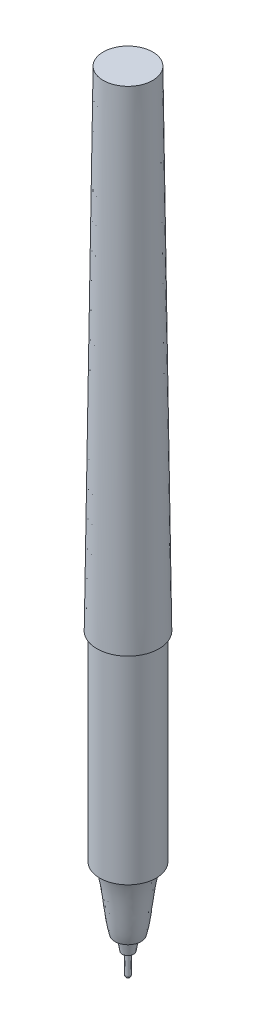
SolidWorks part; units mm, degrees
ref_plane "Front Plane" through (0, 0, 0) normal (0, 0, 1) x (1, 0, 0)
ref_plane "Top Plane" through (0, 0, 0) normal (0, 1, 0) x (1, 0, 0)
ref_plane "Right Plane" through (0, 0, 0) normal (1, 0, 0) x (0, 0, -1)
sketch "Sketch1" plane through (0, 0, 0) normal (0, 1, 0) x (1, 0, 0)
  circle A0 centre (0, 0) radius 4.9911
  dimension "D1" = 9.9822
sketch3d "3DSketch1" plane through (0, 0, 0) normal (0, 0, 1) x (1, 0, 0)
  dimension "D1" = 78.74
sketch "Sketch8" plane through (0, 0, 0) normal (1, 0, 0) x (0, 0, -1)
  line L0 (0, -1000) -> (0, 49000) construction
sketch "Sketch9" plane through (0, 78.74, 0) normal (0, 1, 0) x (-1, 0, 0)
  circle A0 centre (0, 0) radius 3.9782
  dimension "D1" = 7.9565
loft "Loft2" add profiles "Sketch1", "Sketch9"
sketch "Sketch11" plane through (0, 0, 0) normal (0, -1, 0) x (1, 0, 0)
  circle A0 centre (0, 0) radius 4.5466
  dimension "D1" = 9.0932
extrude "Boss-Extrude6" add sketch "Sketch11" along normal blind 32.1945
sketch "Sketch12" plane through (0, 0, 0) normal (0, 0, 1) x (1, 0, 0)
  line L0 (0, -201000) -> (0, 249000) construction
  line L1 (0, -32.1945) -> (3.8608, -32.1945)
  line L2 (-4.5466, -32.1945) -> (4.5466, -32.1945) construction
  line L3 (0, -42.2783) -> (2.1019, -42.2783)
  line L4 (0, -32.1945) -> (0, -42.2783)
  spline S0 degree 3 poles (3.8608, -32.1945) (2.8705, -34.9719) (2.8125, -39.8412) (2.1018, -42.2783) knots 0 0 0 0 1 1 1 1
  dimension "D3" = 10.0838
  dimension "D1" = 3.8608
  dimension "D2" = 2.1019
revolve "Revolve1" add sketch "Sketch12" angle 360 about L0
sketch "Sketch13" plane through (0, 0, 0) normal (0, 0, 1) x (1, 0, 0)
  line L0 (0, -42.2783) -> (1.3144, -42.2783)
  line L1 (-2.1018, -42.2783) -> (2.1018, -42.2783) construction
  line L2 (1.3144, -42.2783) -> (0.9207, -44.6278)
  line L3 (0.9207, -44.6278) -> (0, -44.6278)
  line L4 (0, -201000) -> (0, 249000) construction
  line L5 (0, -42.2783) -> (0, -44.6278)
  dimension "D1" = 1.3144
  dimension "D2" = 0.9207
  dimension "D3" = 2.3495
revolve "Revolve2" add sketch "Sketch13" angle 360 about L0
sketch "Sketch14" plane through (0, 0, 0) normal (0, 0, 1) x (1, 0, 0)
  line L0 (0, -44.6278) -> (0.4001, -44.6278)
  line L1 (0, -201000) -> (0, 249000) construction
  line L2 (0.4001, -44.6278) -> (0.4001, -47.9044)
  line L3 (-0.9207, -44.6278) -> (0.9207, -44.6278) construction
  line L4 (0, -44.6278) -> (0, -48.3108)
  arc A0 (0.4001, -47.9044) -> (0, -48.3108) centre (-0.0063, -47.9044) cw
  dimension "D2" = 0.4064
  dimension "D1" = 0.4001
  dimension "D3" = 3.683
revolve "Revolve3" add sketch "Sketch14" angle 360 about L0
